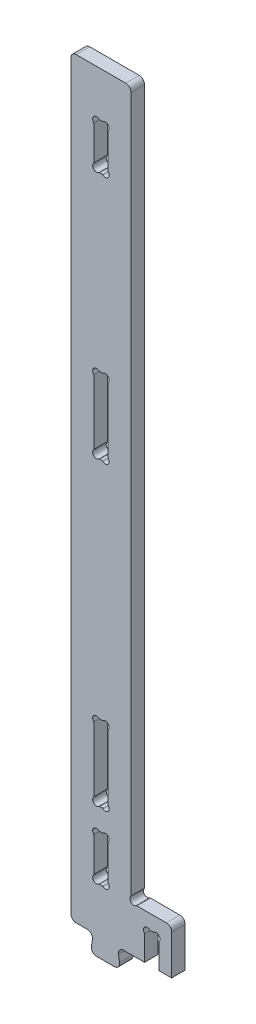
SolidWorks part; units mm, degrees
ref_plane "Front Plane" through (0, 0, 0) normal (0, 0, 1) x (1, 0, 0)
ref_plane "Top Plane" through (0, 0, 0) normal (0, 1, 0) x (1, 0, 0)
ref_plane "Right Plane" through (0, 0, 0) normal (1, 0, 0) x (0, 0, -1)
sketch "Sketch1" plane through (0, 0, 0) normal (0, 0, 1) x (1, 0, 0)
  line L0 (131, 60) -> (131, 0) construction
  line L1 (0, 0) -> (30, 0)
  line L2 (0, 0) -> (0, 1000)
  line L3 (0, 1000) -> (80, 1000)
  line L4 (80, 67.9878) -> (80, 1000)
  line L5 (87.9878, 60) -> (134, 60)
  line L6 (62, 0) -> (134, 0)
  line L7 (30, 0) -> (30, -25) construction
  line L8 (134, 60) -> (134, 0)
  line L9 (30, 0) -> (26, -25)
  line L10 (26, -25) -> (66, -25)
  line L11 (62, 0) -> (66, -25)
  line L12 (62, 0) -> (62, -25) construction
  line L13 (80, 60) -> (83.5355, 63.5355) construction
  arc A0 (79.5118, 66.5037) -> (86.5037, 59.5118) centre (83.5355, 63.5355) ccw
  arc A1 (79.5118, 66.5037) -> (80, 67.9878) centre (77.5, 67.9878) ccw
  arc A2 (86.5037, 59.5118) -> (87.9878, 60) centre (87.9878, 57.5) cw
  dimension "D12" = 5
  dimension "D13" = 2.5
  dimension "D2" = 1000
  dimension "D3" = 54
  dimension "D4" = 60
  dimension "D8" = 4
  dimension "D5" = 25
  dimension "D6" = 30
  dimension "D7" = 4
  dimension "D9" = 40
  dimension "D10" = 45
  dimension "D11" = 80
extrude "Boss-Extrude1" add sketch "Sketch1" along normal blind 18 contours L2 L3 L4 A1 A0 A2 L5 L8 L6 L11 L10 L9 L1
sketch "Sketch2" plane through (0, 0, 0) normal (0, 0, 1) x (1, 0, 0)
  line L0 (40, 60) -> (40, 549.5) construction
  line L1 (0, 1000) -> (80, 1000) construction
  line L2 (80, 67.9878) -> (80, 1000) construction
  line L3 (0, 0) -> (0, 1000) construction
  line L4 (49.5, 642.7488) -> (49.5, 557.2512)
  line L5 (30.5, 600) -> (49.5, 600) construction
  line L6 (30.5, 642.7488) -> (30.5, 557.2512)
  line L7 (38.2512, 549.5) -> (41.7488, 549.5)
  line L8 (38.2512, 650.5) -> (41.7488, 650.5)
  line L9 (30.5, 549.5) -> (40, 559) construction
  line L16 (80, 60) -> (0, 60) construction
  line L24 (80, 60) -> (134, 60) construction
  arc A0 (30.1123, 556.1353) -> (37.1353, 549.1123) centre (34.0355, 553.0355) ccw
  arc A1 (30.1123, 556.1353) -> (30.5, 557.2512) centre (28.7, 557.2512) ccw
  arc A2 (37.1353, 549.1123) -> (38.2512, 549.5) centre (38.2512, 547.7) cw
  arc A3 (42.8647, 549.1123) -> (41.7488, 549.5) centre (41.7488, 547.7) ccw
  arc A5 (49.8877, 556.1353) -> (42.8647, 549.1123) centre (45.9645, 553.0355) cw
  arc A7 (49.8877, 556.1353) -> (49.5, 557.2512) centre (51.3, 557.2512) cw
  arc A8 (49.8877, 643.8647) -> (49.5, 642.7488) centre (51.3, 642.7488) ccw
  arc A9 (49.8877, 643.8647) -> (42.8647, 650.8877) centre (45.9645, 646.9645) ccw
  arc A10 (42.8647, 650.8877) -> (41.7488, 650.5) centre (41.7488, 652.3) cw
  arc A11 (37.1353, 650.8877) -> (38.2512, 650.5) centre (38.2512, 652.3) ccw
  arc A12 (30.1123, 643.8647) -> (37.1353, 650.8877) centre (34.0355, 646.9645) cw
  arc A13 (30.1123, 643.8647) -> (30.5, 642.7488) centre (28.7, 642.7488) cw
  point P21 (40, 549.5)
  dimension "D7" = 5
  dimension "D4" = 1.8
  dimension "D3" = 45
  dimension "D6" = 9.5
  dimension "D1" = 50.5
  dimension "D2" = 400
extrude "Cut-Extrude1" cut sketch "Sketch2" along normal through all
sketch "Sketch3" plane through (0, 0, 0) normal (0, 0, 1) x (1, 0, 0)
  line L0 (107.5, 60) -> (107.5, 0) construction
  line L1 (62, 0) -> (134, 0) construction
  line L2 (98, 0) -> (117, 0)
  line L3 (117, 32.7488) -> (117, 0)
  line L4 (117, 40.5) -> (107.5, 31) construction
  line L5 (105.7512, 40.5) -> (109.2488, 40.5)
  line L9 (98, 32.7488) -> (98, 0)
  line L10 (80, 67.9878) -> (80, 1000) construction
  line L11 (87.9878, 60) -> (134, 60) construction
  arc A0 (117, 32.7488) -> (117.3877, 33.8647) centre (118.8, 32.7488) cw
  arc A1 (117.3877, 33.8647) -> (110.3647, 40.8877) centre (113.4645, 36.9645) ccw
  arc A2 (109.2488, 40.5) -> (110.3647, 40.8877) centre (109.2488, 42.3) ccw
  arc A3 (98, 32.7488) -> (97.6123, 33.8647) centre (96.2, 32.7488) ccw
  arc A4 (97.6123, 33.8647) -> (104.6353, 40.8877) centre (101.5355, 36.9645) cw
  arc A5 (105.7512, 40.5) -> (104.6353, 40.8877) centre (105.7512, 42.3) cw
  point P23 (107.5, 40.5)
  dimension "D4" = 1.8
  dimension "D3" = 5
  dimension "D1" = 45
  dimension "D2" = 9.5
  dimension "D5" = 40.5
  dimension "D6" = 18
extrude "Cut-Extrude2" cut sketch "Sketch3" along normal through all
sketch "Sketch4" plane through (0, 0, 0) normal (0, 0, 1) x (1, 0, 0)
  line L0 (0, 1000) -> (80, 1000) construction
  line L1 (87.9878, 60) -> (134, 60) construction
  line L2 (49.5, 113.2488) -> (49.5, 67.7512)
  line L4 (38.2512, 121) -> (41.7488, 121)
  line L5 (0, 500.25) -> (80, 500.25) construction
  line L6 (0, 0) -> (0, 1000) construction
  line L7 (30.5, 90.5) -> (40, 90.5) construction
  line L8 (30.5, 113.2488) -> (30.5, 67.7512)
  line L9 (80, 67.9878) -> (80, 1000) construction
  line L11 (38.2512, 60) -> (41.7488, 60)
  line L12 (0, 910) -> (80, 910) construction
  line L13 (108.1496, 90.5) -> (108.1496, 910) construction
  line L14 (38.2512, 879.5) -> (41.7488, 879.5)
  line L15 (49.5, 887.2512) -> (49.5, 932.7488)
  line L16 (38.2512, 940.5) -> (41.7488, 940.5)
  line L17 (30.5, 887.2512) -> (30.5, 932.7488)
  line L20 (30.5, 60) -> (40, 69.5) construction
  line L23 (40, 1000) -> (40, 60) construction
  arc A0 (38.2512, 60) -> (37.1353, 59.6123) centre (38.2512, 58.2) ccw
  arc A1 (30.5, 67.7512) -> (30.1123, 66.6353) centre (28.7, 67.7512) cw
  arc A2 (41.7488, 60) -> (42.8647, 59.6123) centre (41.7488, 58.2) cw
  arc A3 (49.8877, 66.6353) -> (42.8647, 59.6123) centre (45.9645, 63.5355) cw
  arc A4 (49.5, 67.7512) -> (49.8877, 66.6353) centre (51.3, 67.7512) ccw
  arc A5 (49.5, 113.2488) -> (49.8877, 114.3647) centre (51.3, 113.2488) cw
  arc A6 (30.1123, 66.6353) -> (37.1353, 59.6123) centre (34.0355, 63.5355) ccw
  arc A7 (49.8877, 114.3647) -> (42.8647, 121.3877) centre (45.9645, 117.4645) ccw
  arc A8 (41.7488, 121) -> (42.8647, 121.3877) centre (41.7488, 122.8) ccw
  arc A9 (38.2512, 121) -> (37.1353, 121.3877) centre (38.2512, 122.8) cw
  arc A10 (30.1123, 114.3647) -> (37.1353, 121.3877) centre (34.0355, 117.4645) cw
  arc A11 (30.5, 113.2488) -> (30.1123, 114.3647) centre (28.7, 113.2488) ccw
  arc A12 (30.5, 887.2512) -> (30.1123, 886.1353) centre (28.7, 887.2512) cw
  arc A13 (30.1123, 886.1353) -> (37.1353, 879.1123) centre (34.0355, 883.0355) ccw
  arc A14 (38.2512, 879.5) -> (37.1353, 879.1123) centre (38.2512, 877.7) ccw
  arc A15 (41.7488, 879.5) -> (42.8647, 879.1123) centre (41.7488, 877.7) cw
  arc A16 (49.8877, 886.1353) -> (42.8647, 879.1123) centre (45.9645, 883.0355) cw
  arc A17 (49.5, 887.2512) -> (49.8877, 886.1353) centre (51.3, 887.2512) ccw
  arc A18 (49.5, 932.7488) -> (49.8877, 933.8647) centre (51.3, 932.7488) cw
  arc A19 (49.8877, 933.8647) -> (42.8647, 940.8877) centre (45.9645, 936.9645) ccw
  arc A20 (41.7488, 940.5) -> (42.8647, 940.8877) centre (41.7488, 942.3) ccw
  arc A21 (38.2512, 940.5) -> (37.1353, 940.8877) centre (38.2512, 942.3) cw
  arc A22 (30.1123, 933.8647) -> (37.1353, 940.8877) centre (34.0355, 936.9645) cw
  arc A23 (30.5, 932.7488) -> (30.1123, 933.8647) centre (28.7, 932.7488) ccw
  point P22 (49.5, 90.5)
  point P39 (40, 60)
  point P50 (108.1496, 500.25)
  dimension "D8" = 5
  dimension "D2" = 1.8
  dimension "D7" = 45
  dimension "D9" = 30.5
  dimension "D10" = 9.5
  dimension "D3" = 90
extrude "Cut-Extrude3" cut sketch "Sketch4" along normal through all
pattern_linear "LPattern1" count 2 spacing 400 along (0, -1, 0) of "Cut-Extrude1"
fillet "Fillet1" radius 7 8 edges at (0, 1000, 9) (80, 1000, 9) (134, 60, 9) (62, 0, 9) (66, -25, 9) (26, -25, 9) (30, 0, 9) (0, 0, 9)
equation "\"tool_diameter\"=9"
equation "\"hole_clearance\"=0.5"
equation "\"material_thickness\"=18"
equation "\"clearance\"=0.5"
equation "\"outer_slot\"=0.5"
equation "\"fillet\"=7"
equation "\"D3@Sketch1\"=\"material_thickness\"*3"
equation "\"D12@Sketch1\"=\"tool_diameter\"/2+\"hole_clearance\""
equation "\"D13@Sketch1\"=\"D12@Sketch1\"/2"
equation "\"D1@Boss-Extrude1\"=\"material_thickness\""
equation "\"D1@Sketch2\"=\"clearance\"+50"
equation "\"D7@Sketch2\"=\"tool_diameter\"/2+\"hole_clearance\""
equation "\"D4@Sketch2\"=\"material_thickness\"/10"
equation "\"D5@Sketch3\"=\"clearance\"+40"
equation "\"D3@Sketch3\"=\"tool_diameter\"/2+\"hole_clearance\""
equation "\"D2@Sketch3\"=\"material_thickness\"/2+\"clearance\""
equation "\"D4@Sketch3\"=\"material_thickness\"/10"
equation "\"D6@Sketch3\"=\"material_thickness\""
equation "\"D8@Sketch4\"=\"tool_diameter\"/2+\"hole_clearance\""
equation "\"D2@Sketch4\"=\"material_thickness\"/10"
equation "\"D9@Sketch4\"=\"clearance\"+30"
equation "\"D10@Sketch4\"=\"material_thickness\"/2+\"clearance\""
equation "\"D6@Sketch2\"=\"material_thickness\"/2+\"clearance\""
equation "\"D1@Fillet1\"=\"fillet\""
equation "\"string\"= 2 * \"tool_diameter\" / 2 * cos ( 45deg )"
equation "\"angle\"= IIF ( \"string\" < \"limit\" , 45 , ( 180 - 2 * arcsin ( \"ThicknessVStool_dia\" ) ) / 2 )"
equation "\"limit\"= \"material_thickness\" / 2 * 9 / 10"
equation "\"ThicknessVStool_dia\"= IIF ( \"limit\" / \"tool_diameter\" > 1 , 1 , \"limit\" / \"tool_diameter\" )"
equation "\"D3@Sketch2\"=\"angle\""
equation "\"D1@Sketch3\"=\"angle\""
equation "\"D7@Sketch4\"=\"angle\""
